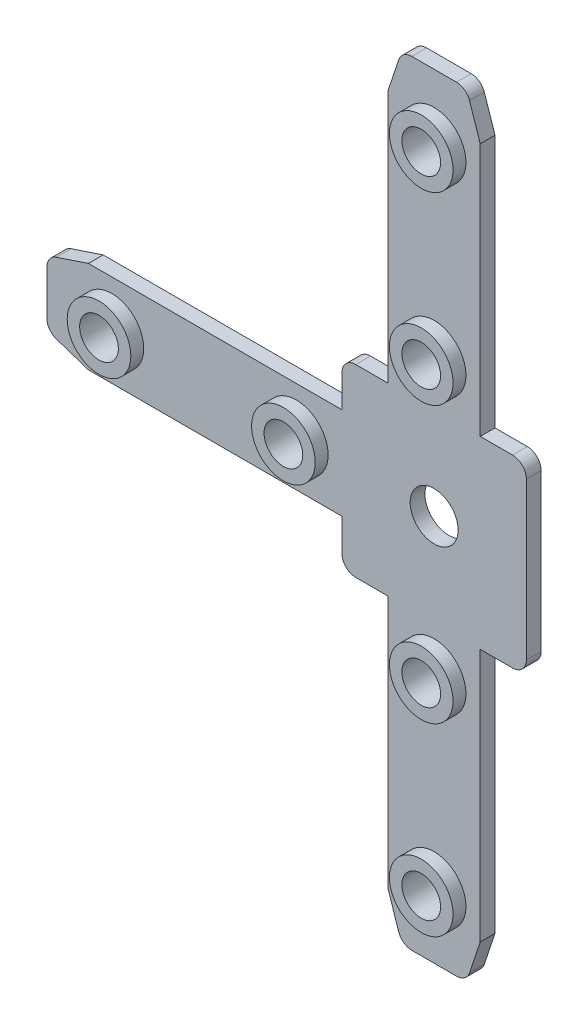
SolidWorks part; units mm, degrees
material "Plain Carbon Steel"
ref_plane "Front Plane" through (0, 0, 0) normal (0, 0, 1) x (1, 0, 0)
ref_plane "Top Plane" through (0, 0, 0) normal (0, 1, 0) x (1, 0, 0)
ref_plane "Right Plane" through (0, 0, 0) normal (1, 0, 0) x (0, 0, -1)
sketch "Sketch1" plane through (0, 0, 0) normal (0, 0, 1) x (1, 0, 0)
  line L0 (-10, 0) -> (0, 0) construction
  line L1 (0, 0) -> (0, 41.985) construction
  line L2 (-10, -8.5) -> (-10, -5)
  line L3 (-8.5, 10) -> (-5, 10)
  line L4 (-5, 10) -> (-5, 37.485)
  line L5 (-5, 37.485) -> (-3.8419, 40.9593)
  line L6 (-2.4189, 41.985) -> (2.4189, 41.985)
  line L7 (5, 37.485) -> (3.8419, 40.9593)
  line L8 (5, 10) -> (5, 37.485)
  line L9 (8.5, 10) -> (5, 10)
  line L10 (10, -8.5) -> (10, 8.5)
  line L11 (8.5, -10) -> (5, -10)
  line L12 (5, -10) -> (5, -37.485)
  line L13 (5, -37.485) -> (3.8419, -40.9593)
  line L14 (-2.4189, -41.985) -> (2.4189, -41.985)
  line L15 (-5, -37.485) -> (-3.8419, -40.9593)
  line L16 (-5, -10) -> (-5, -37.485)
  line L17 (-8.5, -10) -> (-5, -10)
  line L18 (-10, 5) -> (-37.5, 5)
  line L19 (-37.5, 5) -> (-40.9743, 3.8419)
  line L20 (-42, 2.4189) -> (-42, -2.4189)
  line L21 (-37.5, -5) -> (-40.9743, -3.8419)
  line L22 (-10, -5) -> (-37.5, -5)
  line L23 (-10, 5) -> (-10, 8.5)
  circle A0 centre (0, 0) radius 2.6
  arc A1 (-2.4189, -41.985) -> (-3.8419, -40.9593) centre (-2.4189, -40.485) cw
  arc A2 (3.8419, -40.9593) -> (2.4189, -41.985) centre (2.4189, -40.485) cw
  arc A3 (-3.8419, 40.9593) -> (-2.4189, 41.985) centre (-2.4189, 40.485) cw
  arc A4 (3.8419, 40.9593) -> (2.4189, 41.985) centre (2.4189, 40.485) ccw
  arc A5 (-8.5, -10) -> (-10, -8.5) centre (-8.5, -8.5) cw
  arc A6 (-10, 8.5) -> (-8.5, 10) centre (-8.5, 8.5) cw
  arc A7 (8.5, 10) -> (10, 8.5) centre (8.5, 8.5) cw
  arc A8 (8.5, -10) -> (10, -8.5) centre (8.5, -8.5) ccw
  arc A9 (-40.9743, -3.8419) -> (-42, -2.4189) centre (-40.5, -2.4189) cw
  arc A10 (-40.9743, 3.8419) -> (-42, 2.4189) centre (-40.5, 2.4189) ccw
  point P15 (10, 0)
  point P24 (-3.5, -41.985)
  point P27 (3.5, -41.985)
  point P30 (-3.5, 41.985)
  point P33 (3.5, 41.985)
  point P36 (-10, -10)
  point P39 (-10, 10)
  point P42 (10, 10)
  point P45 (10, -10)
  point P51 (-42, 0)
  point P55 (-42, -3.5)
  point P58 (-42, 3.5)
  dimension "D4" = 5.2
  dimension "D8" = 1.5
  dimension "D9" = 10
  dimension "D10" = 32
  dimension "D11" = 4.5
  dimension "D13" = 1.5
  dimension "D1" = 20
  dimension "D2" = 20
  dimension "D3" = 10
  dimension "D5" = 4.5
  dimension "D6" = 83.97
  dimension "D7" = 7
  dimension "D12" = 7
extrude "Boss-Extrude1" add sketch "Sketch1" along normal blind 1.6
sketch "Sketch2" plane through (0, 0, 1.6) normal (0, 0, 1) x (1, 0, 0)
  line L0 (-42, 0) -> (0, 0) construction
  line L2 (0, 0) -> (0, 41.985) construction
  line L3 (2.4189, 41.985) -> (-2.4189, 41.985) construction
  line L4 (-42, 2.4189) -> (-42, -2.4189) construction
  circle A0 centre (0, 14.95) radius 3.45
  circle A1 centre (0, 34.95) radius 3.45
  circle A2 centre (0, -14.95) radius 3.45
  circle A3 centre (0, -34.95) radius 3.45
  circle A4 centre (-14.95, 0) radius 3.45
  circle A5 centre (-34.95, 0) radius 3.45
  circle A6 centre (0, 0) radius 2.6 construction
  dimension "D1" = 6.9
  dimension "D3" = 14.95
  dimension "D5" = 14.95
  dimension "D2" = 20
  dimension "D4" = 20
extrude "Boss-Extrude2" add sketch "Sketch2" along normal blind 1.4
hole_wizard "M5x0.8 Tapped Hole1" positions "Sketch4" profile "Sketch3" tap size "M5x0.8" standard "ANSI Metric" end condition through all
sketch "Sketch4" plane through (0, 0, 3) normal (0, 0, 1) x (1, 0, 0)
  point P0 (0, 34.95)
  point P3 (0, 14.95)
  point P6 (0, -14.95)
  point P9 (0, -34.95)
  point P13 (-14.95, 0)
  point P16 (-34.95, 0)
sketch "Sketch3" plane through (0, 34.95, 3) normal (1, 0, 0) x (0, -1, 0)
  line L0 (0, 0) -> (0, 3)
  line L1 (0, 3) -> (2.1, 3)
  line L2 (2.1, 3) -> (2.1, 0)
  line L5 (2.1, 0) -> (0, 0)
  line L11 (0, -6.35) -> (0, 107.95) construction
  dimension "Thru Tap Drill Dia." = 4.2
  dimension "Thru Tap Drill Depth" = 3
cosmetic thread "Hole Thread1" parameters "D2"=5
cosmetic thread "Hole Thread2" parameters "D2"=5
cosmetic thread "Hole Thread3" parameters "D2"=5
cosmetic thread "Hole Thread4" parameters "D2"=5
cosmetic thread "Hole Thread5" parameters "D2"=5
cosmetic thread "Hole Thread6" parameters "D2"=5
